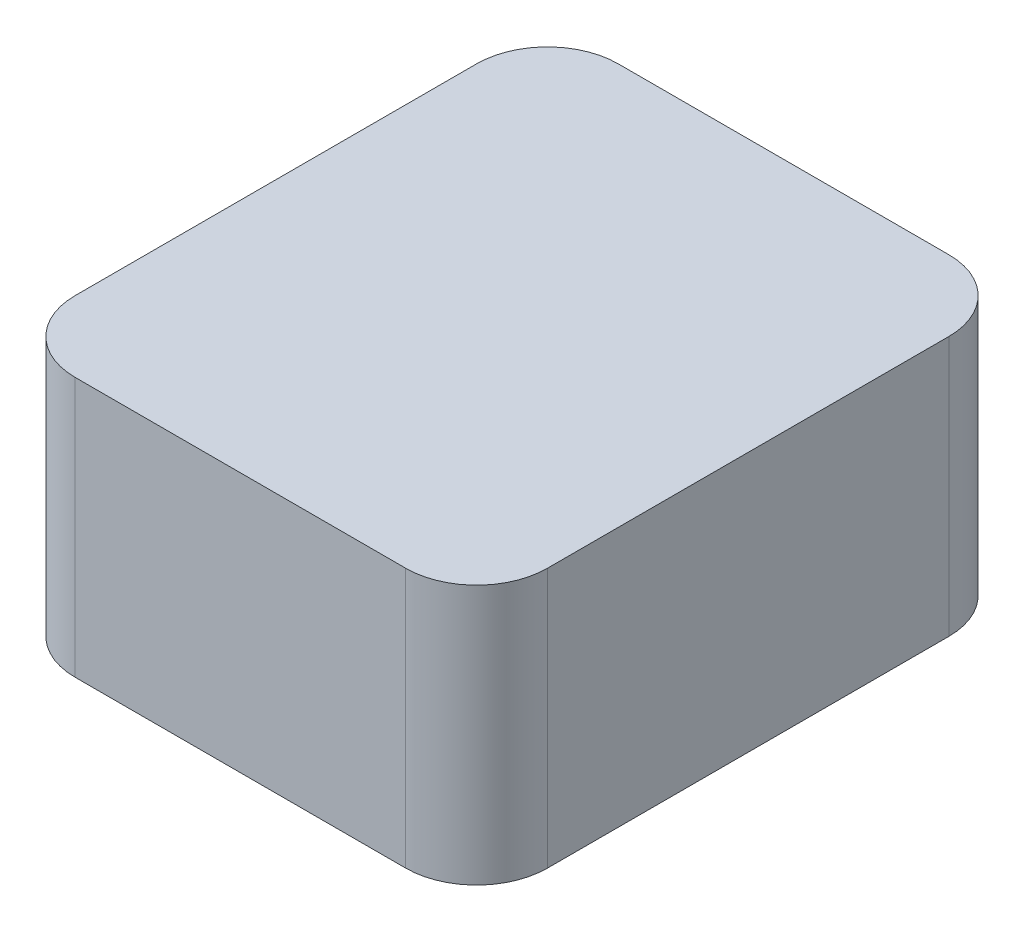
SolidWorks part; units mm, degrees
ref_plane "Front Plane" through (0, 0, 0) normal (0, 0, 1) x (1, 0, 0)
ref_plane "Top Plane" through (0, 0, 0) normal (0, 1, 0) x (1, 0, 0)
ref_plane "Right Plane" through (0, 0, 0) normal (1, 0, 0) x (0, 0, -1)
sketch "Sketch1" plane through (0, 0, 0) normal (0, 1, 0) x (1, 0, 0)
  line L1 (0, 0) -> (20, 0)
  line L2 (0, 0) -> (0, 23)
  line L3 (0, 23) -> (20, 23)
  line L4 (20, 0) -> (20, 23)
  dimension "D1" = 20
  dimension "D2" = 23
extrude "Boss-Extrude1" add sketch "Sketch1" along normal blind 11
fillet "Fillet1" radius 3 4 edges at (20, 5.5, -23) (0, 5.5, -23) (0, 5.5, 0) (20, 5.5, 0)
